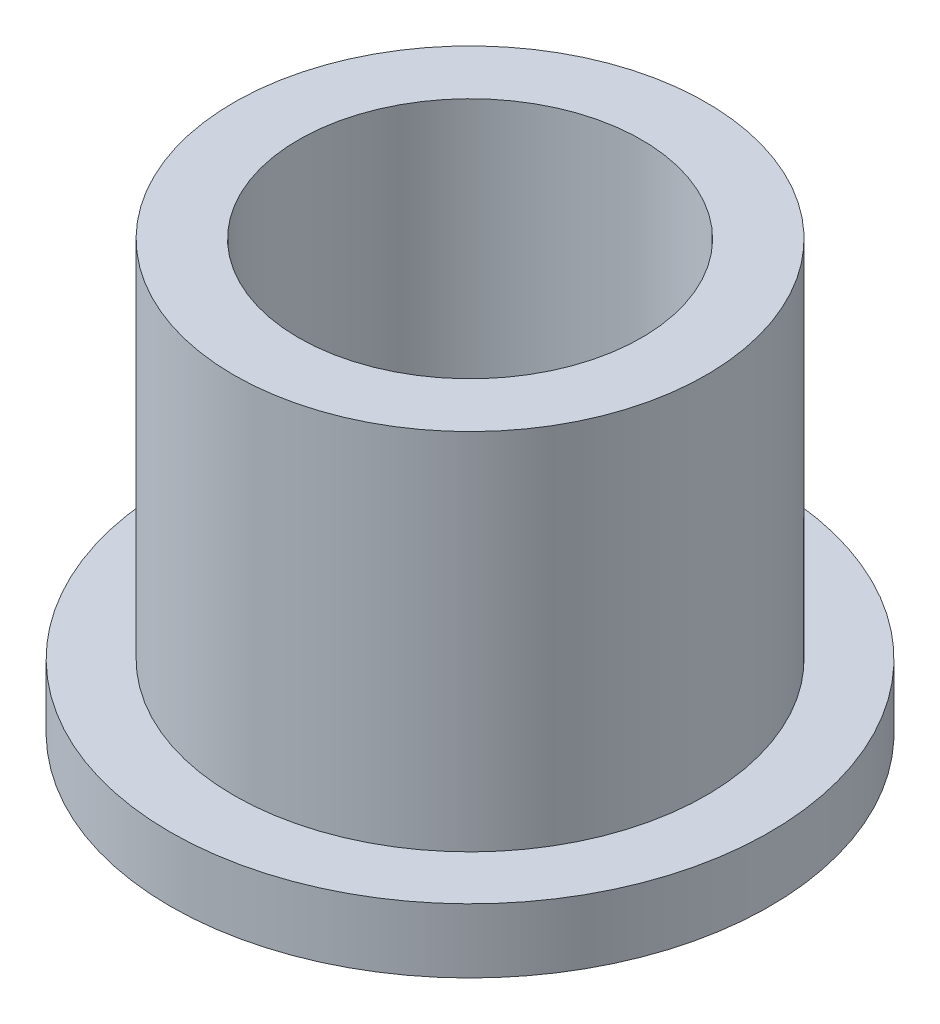
SolidWorks part; units mm, degrees
ref_plane "Front" through (0, 0, 0) normal (0, 0, 1) x (1, 0, 0)
ref_plane "Top" through (0, 0, 0) normal (0, 1, 0) x (1, 0, 0)
ref_plane "Right" through (0, 0, 0) normal (1, 0, 0) x (0, 0, -1)
sketch "Sketch1" plane through (0, 0, 0) normal (0, 1, 0) x (1, 0, 0)
  circle A0 centre (0, 0) radius 4.005
  circle A1 centre (0, 0) radius 5.515
  circle A2 centre (0, 0) radius 7
  dimension "ID" = 8.01
  dimension "OD" = 11.03
  dimension "FlangeOD" = 14
sketch "Sketch2" plane through (0, 0, 0) normal (0, 1, 0) x (1, 0, 0)
  circle A0 centre (0, 0) radius 4.005 construction
  circle A1 centre (0, 0) radius 5.515 construction
  circle A2 centre (0, 0) radius 4.005
  circle A3 centre (0, 0) radius 5.515
extrude "Boss-Extrude1" add sketch "Sketch2" along normal blind 10
sketch "Sketch3" plane through (0, 0, 0) normal (0, 1, 0) x (1, 0, 0)
  circle A0 centre (0, 0) radius 7 construction
  circle A1 centre (0, 0) radius 5.515 construction
  circle A2 centre (0, 0) radius 7
  circle A3 centre (0, 0) radius 5.515
extrude "Boss-Extrude2" add sketch "Sketch3" along normal blind 1.5
